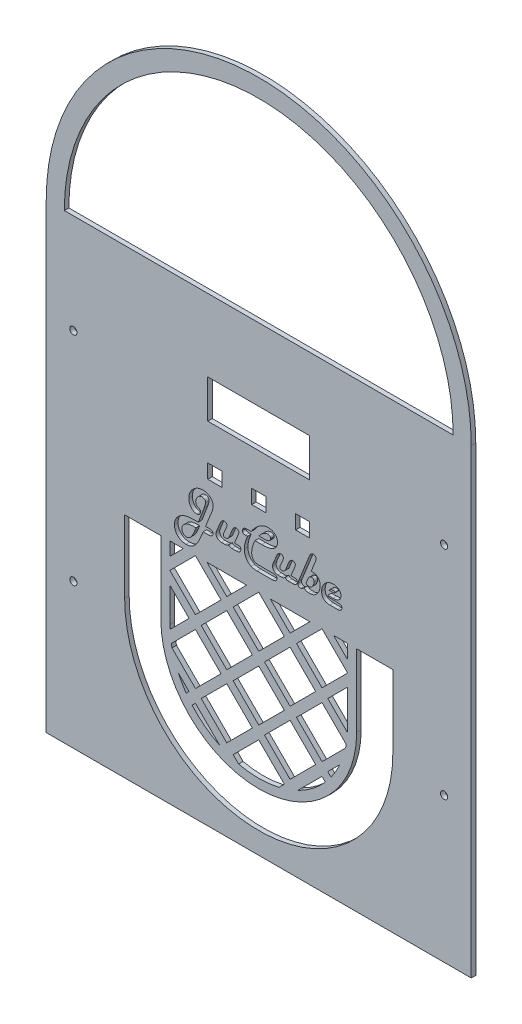
SolidWorks part; units mm, degrees
ref_plane "Front" through (0, 0, 0) normal (0, 0, 1) x (1, 0, 0)
ref_plane "Top" through (0, 0, 0) normal (0, 1, 0) x (1, 0, 0)
ref_plane "Right" through (0, 0, 0) normal (1, 0, 0) x (0, 0, -1)
sketch "Sketch1" plane through (0, 0, 0) normal (0, 0, 1) x (1, 0, 0)
  line L1 (12.7, 0) -> (285.75, 0)
  line L2 (0, 0) -> (0, -323.85)
  line L3 (0, -323.85) -> (298.45, -323.85)
  line L4 (298.45, 0) -> (298.45, -323.85)
  line L5 (113.411, -50.8) -> (185.039, -50.8)
  line L6 (113.411, -50.8) -> (113.411, -77.724)
  line L7 (113.411, -77.724) -> (185.039, -77.724)
  line L8 (185.039, -50.8) -> (185.039, -77.724)
  line L9 (113.411, -103.124) -> (123.317, -103.124)
  line L10 (113.411, -103.124) -> (113.411, -113.03)
  line L11 (113.411, -113.03) -> (123.317, -113.03)
  line L12 (123.317, -103.124) -> (123.317, -113.03)
  line L13 (144.272, -103.124) -> (154.178, -103.124)
  line L14 (144.272, -103.124) -> (144.272, -113.03)
  line L15 (144.272, -113.03) -> (154.178, -113.03)
  line L16 (154.178, -103.124) -> (154.178, -113.03)
  line L17 (175.133, -103.124) -> (185.039, -103.124)
  line L18 (175.133, -103.124) -> (175.133, -113.03)
  line L19 (175.133, -113.03) -> (185.039, -113.03)
  line L20 (185.039, -103.124) -> (185.039, -113.03)
  arc A0 (0, 0) -> (298.45, 0) centre (149.225, 0) cw
  arc A1 (12.7, 0) -> (285.75, 0) centre (149.225, 0) cw
  circle A2 centre (19.05, -69.85) radius 2.54
  circle A3 centre (19.05, -222.25) radius 2.54
  circle A4 centre (279.4, -69.85) radius 2.54
  circle A5 centre (279.4, -222.25) radius 2.54
  point P25 (149.225, -77.724)
  point P26 (149.225, -323.85)
  point P27 (149.225, -103.124)
  dimension "D3" = 12.7
  dimension "D15" = 5.08
  dimension "D17" = 5.08
  dimension "D20" = 5.08
  dimension "D21" = 5.08
  dimension "D1" = 298.45
  dimension "D2" = 323.85
  dimension "D4" = 71.628
  dimension "D5" = 26.924
  dimension "D6" = 9.906
  dimension "D7" = 9.906
  dimension "D8" = 9.906
  dimension "D9" = 9.906
  dimension "D10" = 9.906
  dimension "D11" = 9.906
  dimension "D12" = 25.4
  dimension "D13" = 50.8
  dimension "D14" = 19.05
  dimension "D16" = 19.05
  dimension "D18" = 19.05
  dimension "D19" = 19.05
  dimension "D22" = 152.4
  dimension "D23" = 101.6
  dimension "D24" = 152.4
  dimension "D25" = 101.6
extrude "Boss-Extrude1" add sketch "Sketch1" along normal blind 3.175
sketch "Sketch3" plane through (0, 0, 3.175) normal (0, 0, 1) x (1, 0, 0)
  text T0 "JuCube" font "Harlow Solid Italic" height 25.4
extrude "Cut-Extrude3" cut sketch "Sketch3" against normal blind 2.54
sketch "Sketch4" plane through (0, 0, 3.175) normal (0, 0, 1) x (1, 0, 0)
  line L0 (86.8145, -190.7708) -> (100.2849, -204.2412)
  line L1 (86.8145, -163.83) -> (211.6355, -163.83)
  line L2 (86.8145, -163.83) -> (86.8145, -214.63)
  line L4 (211.6355, -163.83) -> (211.6355, -214.63)
  line L5 (144.272, -113.03) -> (154.178, -113.03) construction
  line L6 (104.775, -163.83) -> (86.8145, -181.7905)
  line L7 (86.8145, -181.7905) -> (104.775, -199.751)
  line L8 (104.775, -199.751) -> (122.7355, -181.7905)
  line L9 (122.7355, -181.7905) -> (104.775, -163.83)
  line L10 (149.225, -199.751) -> (167.1855, -181.7905)
  line L11 (167.1855, -181.7905) -> (149.225, -163.83)
  line L12 (149.225, -163.83) -> (131.2645, -181.7905)
  line L13 (131.2645, -181.7905) -> (149.225, -199.751)
  line L14 (193.675, -199.751) -> (211.6355, -181.7905)
  line L15 (211.6355, -181.7905) -> (193.675, -163.83)
  line L16 (193.675, -163.83) -> (175.7145, -181.7905)
  line L17 (175.7145, -181.7905) -> (193.675, -199.751)
  line L18 (149.225, -244.6523) -> (167.1855, -226.6918)
  line L19 (167.1855, -226.6918) -> (149.225, -208.7313)
  line L20 (149.225, -208.7313) -> (131.2645, -226.6918)
  line L21 (131.2645, -226.6918) -> (149.225, -244.6523)
  line L22 (193.675, -244.6523) -> (210.1467, -228.1806)
  line L23 (210.6456, -225.7018) -> (193.675, -208.7313)
  line L24 (193.675, -208.7313) -> (175.7145, -226.6918)
  line L25 (175.7145, -226.6918) -> (193.675, -244.6523)
  line L26 (163.3598, -275.4188) -> (167.1855, -271.5931)
  line L27 (167.1855, -271.5931) -> (149.225, -253.6326)
  line L28 (149.225, -253.6326) -> (131.2645, -271.5931)
  line L29 (131.2645, -271.5931) -> (135.0902, -275.4188)
  line L31 (195.9955, -255.953) -> (193.675, -253.6326)
  line L32 (193.675, -253.6326) -> (176.5828, -270.7248)
  line L34 (104.775, -244.6523) -> (122.7355, -226.6918)
  line L35 (122.7355, -226.6918) -> (104.775, -208.7313)
  line L36 (104.775, -208.7313) -> (87.8044, -225.7018)
  line L37 (88.3033, -228.1806) -> (104.775, -244.6523)
  line L39 (121.8672, -270.7248) -> (104.775, -253.6326)
  line L40 (104.775, -253.6326) -> (102.4545, -255.953)
  line L42 (100.2849, -204.2412) -> (86.8871, -217.639)
  line L45 (108.8138, -204.2412) -> (126.7744, -186.2806)
  line L46 (126.7744, -186.2806) -> (144.7349, -204.2412)
  line L47 (126.7744, -222.2017) -> (108.8138, -204.2412)
  line L48 (144.7349, -204.2412) -> (126.7744, -222.2017)
  line L49 (153.2638, -204.2412) -> (171.2244, -186.2806)
  line L50 (171.2244, -186.2806) -> (189.1849, -204.2412)
  line L51 (171.2244, -222.2017) -> (153.2638, -204.2412)
  line L52 (189.1849, -204.2412) -> (171.2244, -222.2017)
  line L53 (197.7138, -204.2412) -> (211.6355, -190.3195)
  line L55 (211.5407, -218.068) -> (197.7138, -204.2412)
  line L59 (126.7744, -177.7517) -> (112.8527, -163.83)
  line L60 (140.696, -163.83) -> (126.7744, -177.7517)
  line L63 (171.2244, -177.7517) -> (157.3027, -163.83)
  line L64 (185.146, -163.83) -> (171.2244, -177.7517)
  line L67 (211.6355, -173.7128) -> (201.7527, -163.83)
  line L72 (96.246, -163.83) -> (86.8145, -173.2615)
  line L73 (108.8138, -204.2412) -> (126.7744, -186.2806)
  line L74 (126.7744, -186.2806) -> (144.7349, -204.2412)
  line L75 (126.7744, -222.2017) -> (108.8138, -204.2412)
  line L76 (144.7349, -204.2412) -> (126.7744, -222.2017)
  line L77 (153.2638, -204.2412) -> (171.2244, -186.2806)
  line L78 (171.2244, -186.2806) -> (189.1849, -204.2412)
  line L79 (171.2244, -222.2017) -> (153.2638, -204.2412)
  line L80 (189.1849, -204.2412) -> (171.2244, -222.2017)
  line L81 (197.7138, -204.2412) -> (211.6355, -190.3195)
  line L83 (211.5407, -218.068) -> (197.7138, -204.2412)
  line L85 (108.8138, -248.6912) -> (126.7744, -230.7306)
  line L86 (126.7744, -230.7306) -> (144.7349, -248.6912)
  line L87 (126.7744, -266.6517) -> (108.8138, -248.6912)
  line L88 (144.7349, -248.6912) -> (126.7744, -266.6517)
  line L89 (153.2638, -248.6912) -> (171.2244, -230.7306)
  line L90 (171.2244, -230.7306) -> (189.1849, -248.6912)
  line L91 (171.2244, -266.6517) -> (153.2638, -248.6912)
  line L92 (189.1849, -248.6912) -> (171.2244, -266.6517)
  line L93 (197.7138, -248.6912) -> (206.1176, -240.2874)
  line L95 (199.9761, -250.9535) -> (197.7138, -248.6912)
  line L98 (92.7166, -241.1229) -> (100.2849, -248.6912)
  line L100 (100.2849, -248.6912) -> (98.2862, -250.6898)
  line L101 (104.775, -289.5536) -> (122.7355, -271.5931) [skipped]
  line L102 (86.8145, -271.5931) -> (104.775, -289.5536) [skipped]
  line L105 (175.7145, -271.5931) -> (193.675, -289.5536) [skipped]
  line L106 (193.675, -289.5536) -> (211.6355, -271.5931) [skipped]
  line L107 (233.6349, -248.6912) -> (215.6744, -266.6517) [skipped]
  line L108 (215.6744, -230.7306) -> (233.6349, -248.6912) [skipped]
  line L109 (233.6349, -204.2412) -> (215.6744, -222.2017) [skipped]
  line L110 (233.6349, -204.2412) -> (215.6744, -222.2017) [skipped]
  line L111 (215.6744, -186.2806) -> (233.6349, -204.2412) [skipped]
  line L112 (215.6744, -186.2806) -> (233.6349, -204.2412) [skipped]
  line L115 (82.3244, -141.8306) -> (100.2849, -159.7912) [skipped]
  line L117 (126.7744, -141.8306) -> (144.7349, -159.7912) [skipped]
  line L118 (171.2244, -141.8306) -> (189.1849, -159.7912) [skipped]
  line L119 (215.6744, -141.8306) -> (233.6349, -159.7912) [skipped]
  line L120 (233.6349, -159.7912) -> (215.6744, -177.7517) [skipped]
  arc A0 (86.8145, -214.63) -> (211.6355, -214.63) centre (149.225, -214.63) ccw
  point P7 (149.225, -163.83)
  point P8 (149.225, -113.03)
  dimension "D1" = 124.821
  dimension "D2" = 50.8
  dimension "D3" = 50.8
  dimension "D4" = 25.4
  dimension "D5" = 25.4
  dimension "D6" = 45
  dimension "D10" = 3
  dimension "D11" = 6.35
  dimension "D12" = 6.35
  dimension "D7" = 3
  dimension "D13" = 2
  dimension "D14" = 2
extrude "Cut-Extrude4" cut sketch "Sketch4" against normal through all contours L8 L9 L6 L7 | L48 L46 L45 L47 | L12 L13 L10 L11 | L60 L1 L59 | L64 L1 L63 | L16 L17 L14 L15 | L67 L4 L1 | L52 L50 L49 L51 | L55 A0 L4 L53 | L22 A0 L23 L24 L25 | L95 A0 L93 | L32 A0 L31 | L92 L90 L89 L91 | L20 L21 L18 L19 | L36 A0 L37 L34 L35 | L2 A0 L42 L0 | L72 L1 L2 | L88 L86 L85 L87 | L29 A0 L26 L27 L28 | L40 A0 L39 | L98 A0 L100
sketch "Sketch5" plane through (0, 0, 3.175) normal (0, 0, 1) x (1, 0, 0)
  line L2 (80.4645, -163.83) -> (80.4645, -214.63)
  line L4 (217.9855, -163.83) -> (217.9855, -214.63)
  line L5 (86.8145, -163.83) -> (86.8145, -173.2615) construction
  line L6 (217.9855, -163.83) -> (243.3855, -163.83)
  line L7 (55.0645, -163.83) -> (80.4645, -163.83)
  line L8 (55.0645, -163.83) -> (55.0645, -214.63)
  line L10 (243.3855, -163.83) -> (243.3855, -214.63)
  arc A0 (80.4645, -214.63) -> (217.9855, -214.63) centre (149.225, -214.63) ccw
  arc A1 (55.0645, -214.63) -> (243.3855, -214.63) centre (149.225, -214.63) ccw
  point P4 (0, 0)
  dimension "D2" = 6.35
  dimension "D3" = 50.8
  dimension "D4" = 25.4
extrude "Cut-Extrude5" cut sketch "Sketch5" against normal blind 25.4
